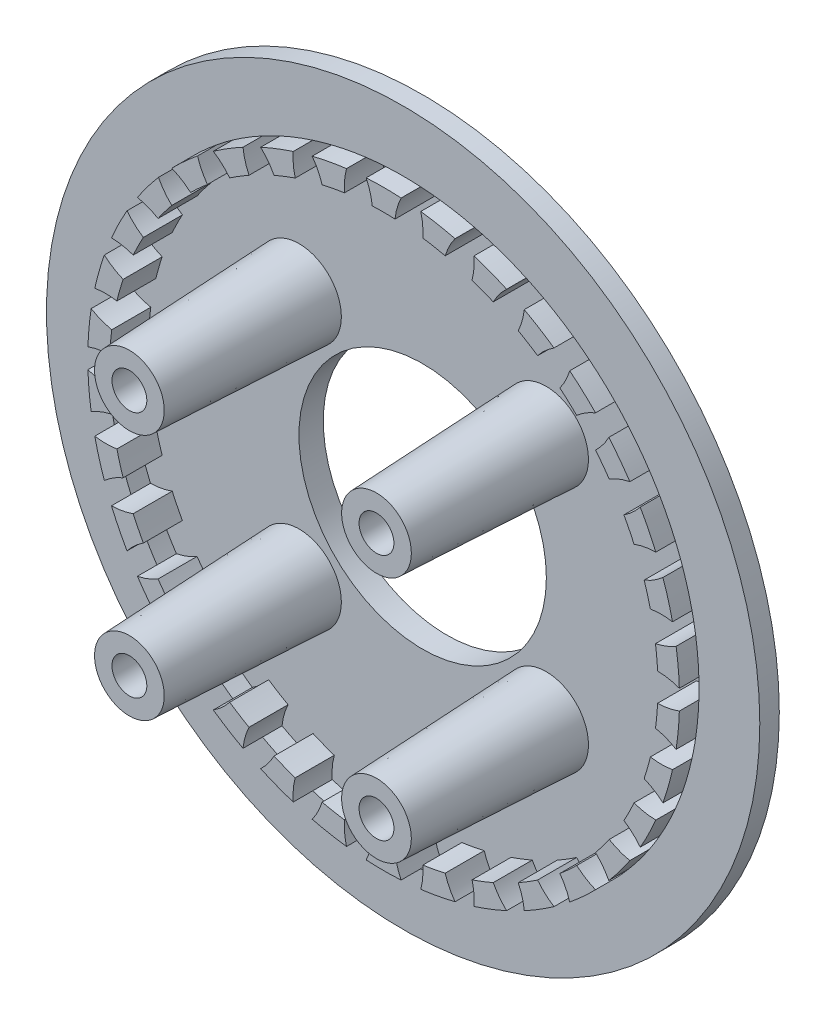
SolidWorks part; units mm, degrees
ref_plane "Front Plane" through (0, 0, 0) normal (0, 0, 1) x (1, 0, 0)
ref_plane "Top Plane" through (0, 0, 0) normal (0, 1, 0) x (1, 0, 0)
ref_plane "Right Plane" through (0, 0, 0) normal (1, 0, 0) x (0, 0, -1)
sketch "Sketch2" plane through (0, 0, 0) normal (0, 0, 1) x (1, 0, 0)
  circle A0 centre (0, 0) radius 54.85
  dimension "D1" = 109.7
extrude "Boss-Extrude1" add sketch "Sketch2" along normal blind 3
sketch "Sketch3" plane through (0, 0, 0) normal (0, 0, -1) x (-1, 0, 0)
  circle A0 centre (0, 0) radius 47.005
  dimension "D1" = 94.01
extrude "Boss-Extrude2" add sketch "Sketch3" along normal blind 3.74
sketch "Sketch4" plane through (0, 0, 3) normal (0, 0, 1) x (1, 0, 0)
  circle A0 centre (0, 0) radius 19.025
  dimension "D1" = 38.05
extrude "Cut-Extrude1" cut sketch "Sketch4" against normal through all
sketch "Sketch5" plane through (0, 0, 3) normal (0, 0, 1) x (1, 0, 0)
  circle A0 centre (0, 0) radius 45.5
  dimension "D1" = 91
extrude "Cut-Extrude2" cut sketch "Sketch5" against normal blind 3
sketch "Sketch6" plane through (0, 0, 0) normal (0, 0, 1) x (1, 0, 0)
  circle A0 centre (-19, 19) radius 6.5
  circle A1 centre (19, 19) radius 6.5
  circle A2 centre (-19, -19) radius 6.5
  circle A3 centre (19, -19) radius 6.5
  point P0 (0, 0)
  dimension "D3" = 13
  dimension "D4" = 13
  dimension "D5" = 13
  dimension "D6" = 13
  dimension "D1" = 38
  dimension "D2" = 38
extrude "Boss-Extrude3" add sketch "Sketch6" along normal blind 26.1 draft 2.5
sketch "Sketch10" plane through (0, 0, 26.1) normal (0, 0, 1) x (1, 0, 0)
  circle A0 centre (19, -19) radius 2.6803
  point P3 (0, 0)
extrude "Cut-Extrude3" cut sketch "Sketch10" against normal through all
pattern_circular "CirPattern1" count 4 over 360 about axis through (0, 0, 0) along (0, 0, 1) of "Cut-Extrude3"
sketch "Sketch17" plane through (0, 0, 0) normal (0, 0, 1) x (1, 0, 0)
  line L0 (0, 0) -> (0, -50000) construction
  line L1 (0, 0) -> (-50000, 0) construction
  line L2 (0, 0) -> (17101.0072, 46984.631) construction
  line L3 (0, 0) -> (-17101.0072, 46984.631) construction
  circle A0 centre (0, 0) radius 45.5
  circle A1 centre (0, 0) radius 42.185
  arc A2 (-2.685, 45.4207) -> (-1.75, 42.1487) centre (-11.6924, 41.0772) cw
  arc A3 (2.685, 45.4207) -> (1.75, 42.1487) centre (11.6924, 41.0772) ccw
  arc A4 (-2.685, 45.4207) -> (2.685, 45.4207) centre (0, 0) cw
  arc A5 (-1.75, 42.1487) -> (1.75, 42.1487) centre (0, 0) cw
  dimension "D1" = 84.37
  dimension "D6" = 10
  dimension "D7" = 10
  dimension "D8" = 91
  dimension "D2" = 20
  dimension "D3" = 20
  dimension "D4" = 5.37
  dimension "D5" = 3.5
extrude "Boss-Extrude7" add sketch "Sketch17" along normal blind 6 contours A2 A5 A3 A4
pattern_circular "CirPattern3" count 34 over 360 about axis through (0, 0, 0) along (0, 0, 1) of "Boss-Extrude7"
